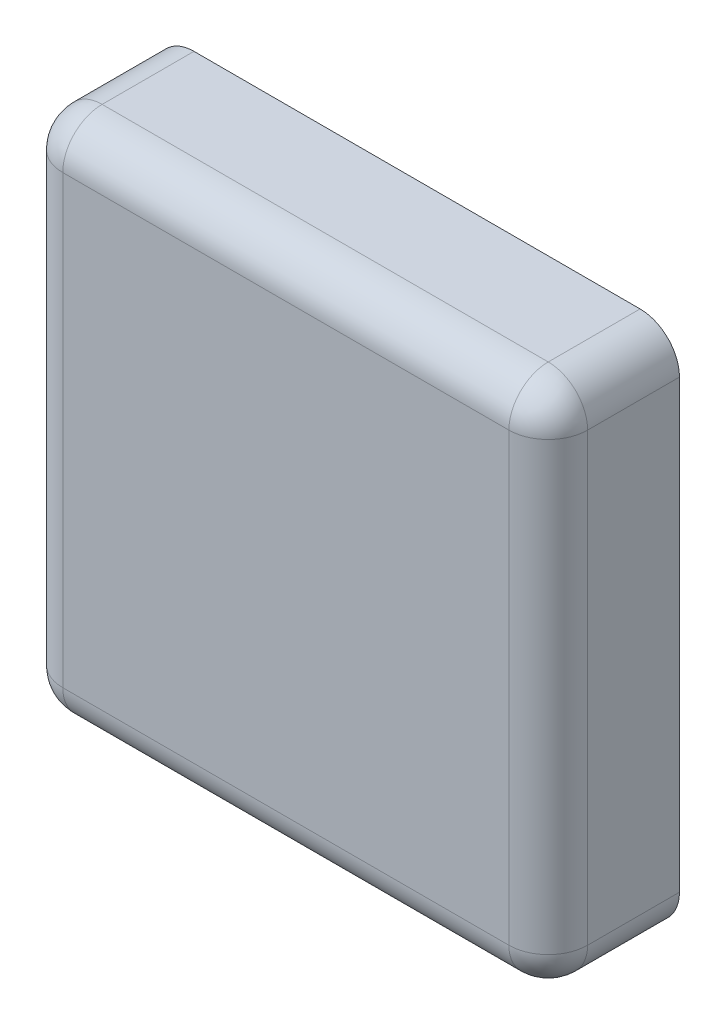
SolidWorks part; units mm, degrees
ref_plane "Front Plane" through (0, 0, 0) normal (0, 0, 1) x (1, 0, 0)
ref_plane "Top Plane" through (0, 0, 0) normal (0, 1, 0) x (1, 0, 0)
ref_plane "Right Plane" through (0, 0, 0) normal (1, 0, 0) x (0, 0, -1)
sketch "Sketch1" plane through (0, 0, 0) normal (0, 0, 1) x (1, 0, 0)
  line L1 (0, 0) -> (-40, 0)
  line L2 (0, 0) -> (0, 40)
  line L3 (0, 40) -> (-40, 40)
  line L4 (-40, 0) -> (-40, 40)
  dimension "D1" = 40
  dimension "D2" = 40
extrude "Boss-Extrude1" add sketch "Sketch1" along normal mid plane 10
fillet "Fillet1" radius 3 8 edges at (-20, 0, 5) (-40, 20, 5) (-20, 40, 5) (0, 20, 5) (0, 40, 0) (-40, 40, 0) (-40, 0, 0) (0, 0, 0)
